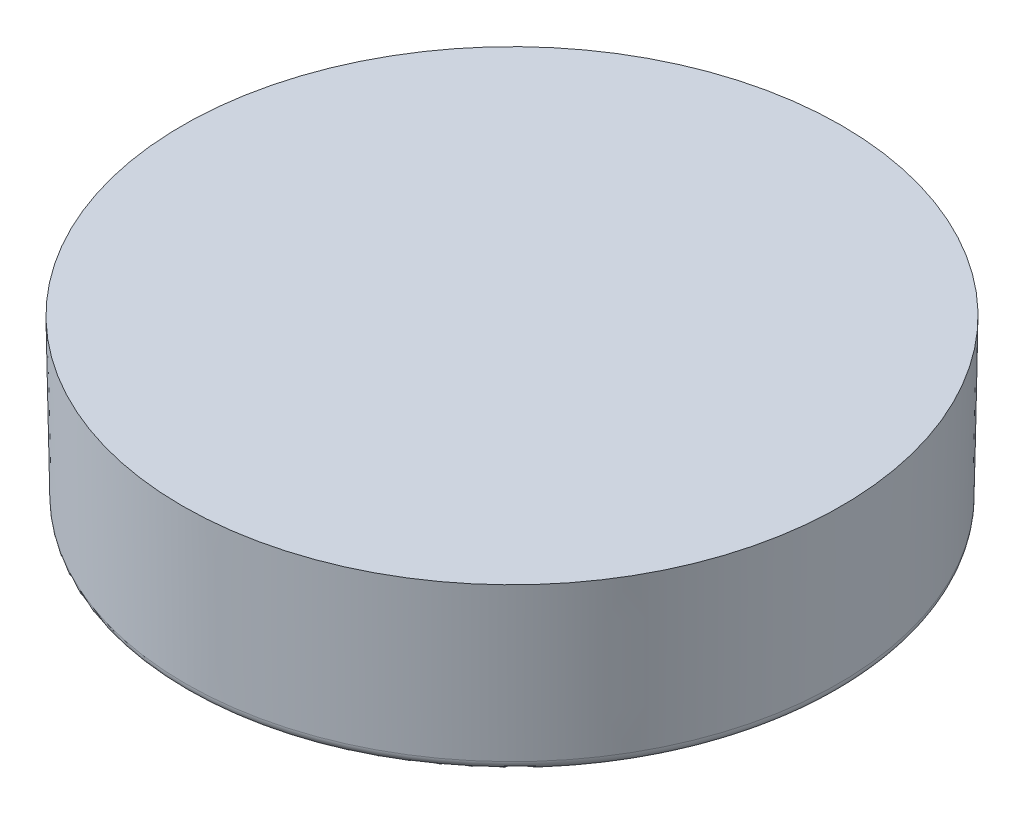
SolidWorks part; units mm, degrees
material "CA"
ref_plane "Front Plane" through (0, 0, 0) normal (0, 0, 1) x (1, 0, 0)
ref_plane "Top Plane" through (0, 0, 0) normal (0, 1, 0) x (1, 0, 0)
ref_plane "Right Plane" through (0, 0, 0) normal (1, 0, 0) x (0, 0, -1)
sketch "Sketch1" plane through (0, 0, 0) normal (0, 1, 0) x (1, 0, 0)
  circle A0 centre (0, 0) radius 12.7
  dimension "D1" = 25.4
extrude "Boss-Extrude1" add sketch "Sketch1" against normal blind 2.3114 draft 1
sketch "Sketch6" plane through (0, 0, 0) normal (0, 0, 1) x (1, 0, 0)
  line L0 (0, 0) -> (0, -2.54) construction
  line L1 (0, -2.54) -> (-6.985, -9.525)
  line L2 (0, -2.54) -> (6.985, -9.525)
  line L3 (-6.985, -9.525) -> (6.985, -9.525)
  line L5 (12.7, 0) -> (-12.7, 0) construction
  dimension "D1" = 2.54
  dimension "D2" = 90
  dimension "D3" = 9.525
sketch "Sketch7" plane through (0, 0, 0) normal (0, 1, 0) x (1, 0, 0)
  circle A1 centre (0, 0) radius 12.7
  circle A2 centre (0, 0) radius 12.7
  circle A3 centre (0, 0) radius 10.922
  circle A4 centre (0, 0) radius 10.922
  dimension "D1" = 0
  dimension "D2" = 1.778
extrude "Boss-Extrude3" add sketch "Sketch7" against normal blind 6.35 draft 1
draft "Draft1" type of draft neutral plane draft angle 10 faces to draft 1 face at (0, -6.35, 11.0328) neutral plane through (0, -2.3114, 0) neutral plane normal (0, -1, 0) parameters "D1"=10
fillet "Fillet2" radius 0.381 2 edges at (0, -6.35, 11.6745) (0, -6.35, 12.5892)
sketch "Sketch11 - OFFSET .005" plane through (0, 0, 0) normal (0, 1, 0) x (1, 0, 0)
  circle A1 centre (0, 0) radius 12.827
  circle A2 centre (0, 0) radius 12.827
  dimension "D1" = 0.127
